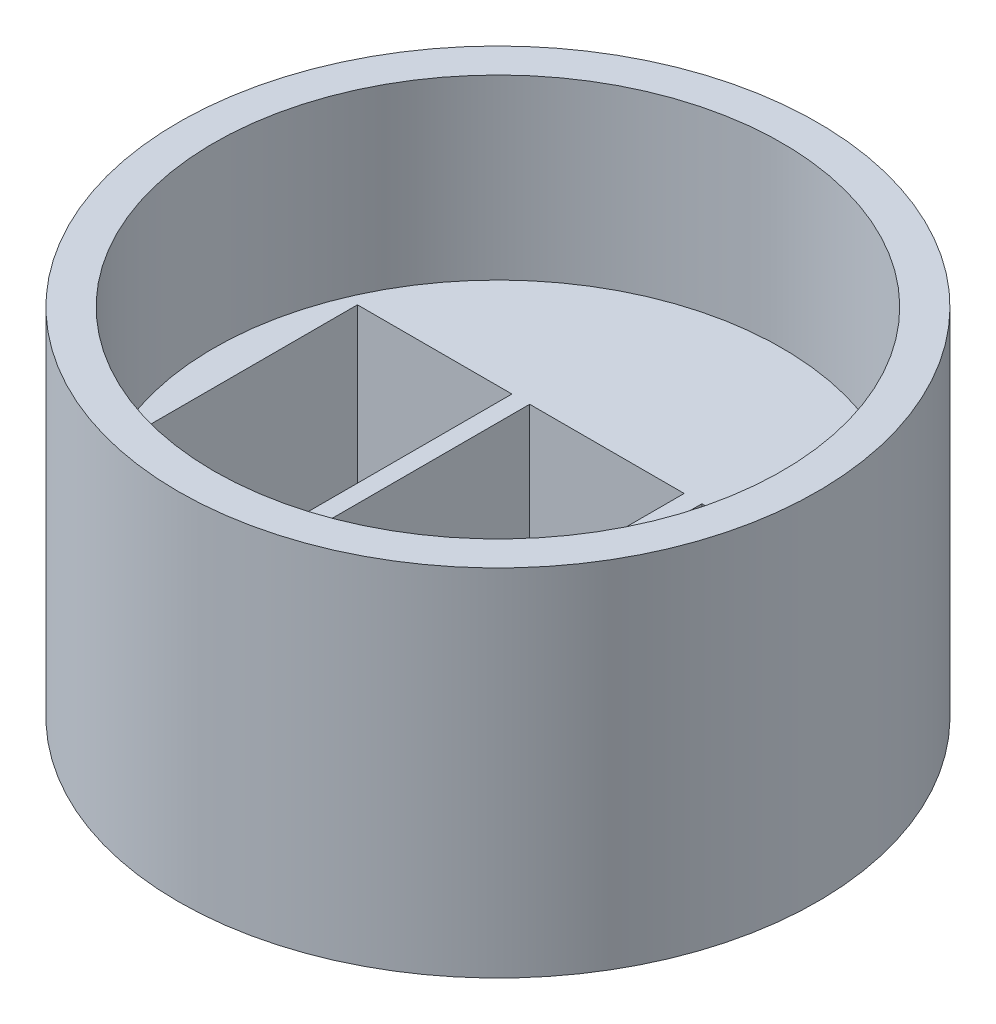
SolidWorks part; units mm, degrees
ref_plane "Front Plane" through (0, 0, 0) normal (0, 0, 1) x (1, 0, 0)
ref_plane "Top Plane" through (0, 0, 0) normal (0, 1, 0) x (1, 0, 0)
ref_plane "Right Plane" through (0, 0, 0) normal (1, 0, 0) x (0, 0, -1)
sketch "Sketch2" plane through (0, 0, 0) normal (0, 1, 0) x (1, 0, 0)
  circle A0 centre (0, 0) radius 9
  dimension "D1" = 18
extrude "Boss-Extrude2" add sketch "Sketch2" along normal blind 10
sketch "Sketch3" plane through (0, 10, 0) normal (0, 1, 0) x (1, 0, 0)
  circle A0 centre (0, 0) radius 8
  dimension "D1" = 16
extrude "Cut-Extrude1" cut sketch "Sketch3" against normal blind 5
sketch "Sketch4" plane through (0, 5, 0) normal (0, 1, 0) x (1, 0, 0)
  line L0 (-8, 0) -> (8, 0) construction
  line L2 (2.1689, -3.075) -> (-2.1811, -3.075)
  line L3 (2.1689, -3.075) -> (2.1689, 3.075)
  line L4 (2.1689, 3.075) -> (-2.1811, 3.075)
  line L5 (-2.1811, -3.075) -> (-2.1811, 3.075)
  line L6 (2.1689, -3.075) -> (-2.1811, 3.075) construction
  line L7 (2.1689, 3.075) -> (-2.1811, -3.075) construction
  line L8 (-7.0311, 3.075) -> (-2.6811, 3.075)
  line L9 (-7.0311, 3.075) -> (-7.0311, -3.075)
  line L10 (-7.0311, -3.075) -> (-2.6811, -3.075)
  line L11 (-2.6811, 3.075) -> (-2.6811, -3.075)
  line L12 (-7.0311, 3.075) -> (-2.6811, -3.075) construction
  line L13 (-7.0311, -3.075) -> (-2.6811, 3.075) construction
  line L14 (7.0189, -3.075) -> (2.6689, -3.075)
  line L15 (7.0189, -3.075) -> (7.0189, 3.075)
  line L16 (7.0189, 3.075) -> (2.6689, 3.075)
  line L17 (2.6689, -3.075) -> (2.6689, 3.075)
  line L18 (7.0189, -3.075) -> (2.6689, 3.075) construction
  line L19 (7.0189, 3.075) -> (2.6689, -3.075) construction
  circle A0 centre (0, 0) radius 8 construction
  circle A1 centre (0, 0) radius 8 construction
  point P7 (-0.0061, 0)
  point P12 (-4.8561, 0)
  point P17 (4.8439, 0)
  dimension "D1" = 4.35
  dimension "D2" = 6.15
  dimension "D3" = 4.35
  dimension "D4" = 6.15
  dimension "D5" = 0.5
  dimension "D6" = 4.35
  dimension "D7" = 6.15
  dimension "D8" = 0.5
extrude "Cut-Extrude2" cut sketch "Sketch4" against normal through all
